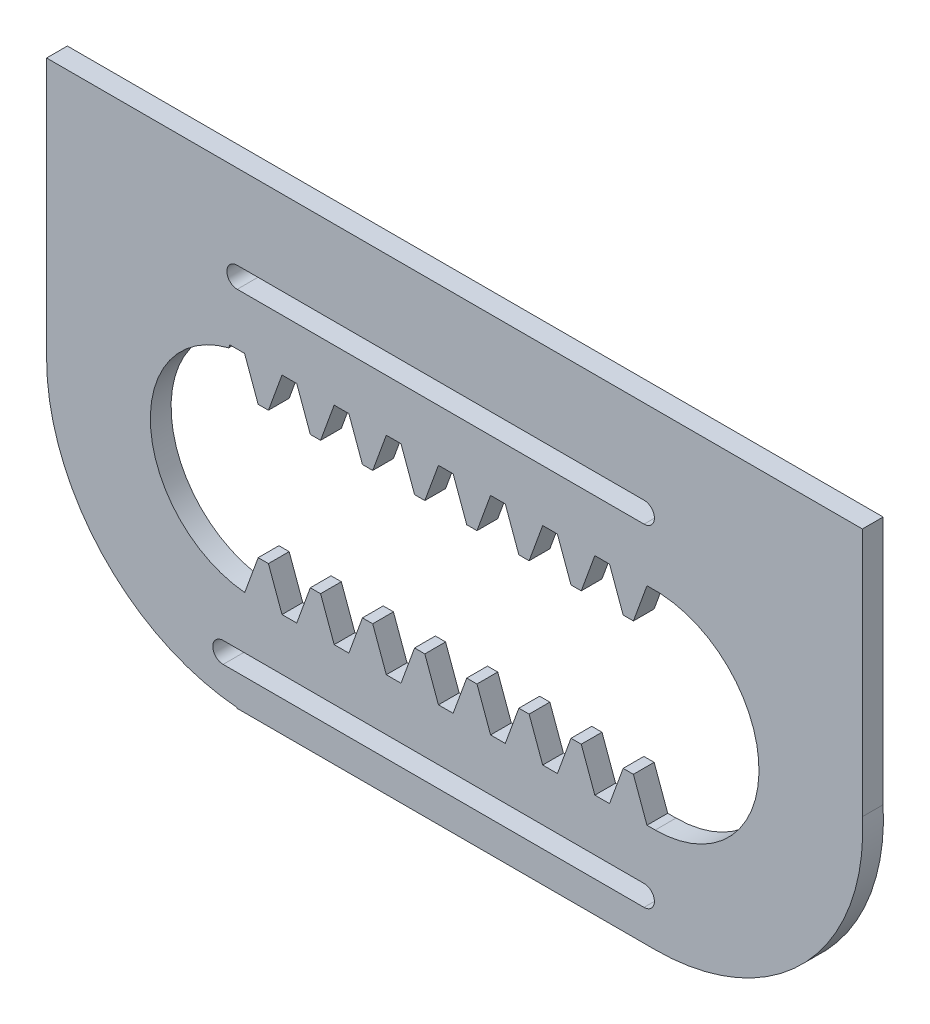
SolidWorks part; units mm, degrees
extrude "Blank" add sketch "BlankSke" against normal blind 25.4
sketch "BlankSke" plane through (0, 0, 0) normal (0, 0, 1) x (1, 0, 0)
  line L1 (0, 0) -> (127, 0)
  line L2 (0, 0) -> (0, 43.18)
  line L3 (0, 43.18) -> (127, 43.18)
  line L4 (127, 0) -> (127, 43.18)
  dimension "Length" = 127
  dimension "Blank_height" = 43.18
ref_plane "Plane1" through (0, 0, 0) normal (0, 0, 1) x (1, 0, 0)
ref_plane "Plane2" through (0, 0, 0) normal (0, 1, 0) x (1, 0, 0)
ref_plane "Plane3" through (0, 0, 0) normal (1, 0, 0) x (0, 0, -1)
other "Configuration Table"
sketch "HoldingSke" plane through (0, 0, 0) normal (0, 1, 0) x (1, 0, 0)
  line L0 (0, 0) -> (97.2876, -81.634)
  line L1 (-15, 0) -> (100, 0) construction
  line L2 (0, 0) -> (-2.1039, 2.3779)
  line L3 (0, 0) -> (-11.863, 4.5341)
  line L4 (0, 0) -> (8.5297, 1.351)
  line L5 (0, 0) -> (-23.7986, -8.8762)
  line L6 (0, 0) -> (-10.5278, -7.1032)
  line L9 (-71.009, 38.7566) -> (48.332, 82.1932)
  line L10 (-76.2, 71.12) -> (-38.1, 71.12)
  line L11 (0, 0) -> (-25.4, 0)
  line L12 (-76.2, 101.6) -> (-76.0095, 101.6)
  line L13 (24.9733, 27.94) -> (52.9518, 28.4284)
  line L14 (24.9733, 27.94) -> (24.9746, 27.94)
  line L15 (24.9733, 27.94) -> (100.4006, 29.5858)
  circle A0 centre (0, 0) radius 19.05
  circle A1 centre (0, 0) radius 19.05
  circle A2 centre (0, 0) radius 12.7
  dimension "MPH" = 38.1
  dimension "Diameter" = 38.1
  dimension "Num_teeth" = 9
  dimension "Pitch" = 127
  dimension "Show_teeth" = 400
  dimension "Thickness" = 12.7
  dimension "Ap" = 20
  dimension "Pitch_height" = 38.1
  dimension "Width" = 25.4
  dimension "Backlash" = 0.1905
  dimension "Addendum_fac" = 1
  dimension "Dedendum_fac" = 1.25
  dimension "Clearance_fac" = 0.25
  dimension "Dedendum_add" = 0.0013
  dimension "Length" = 127
sketch "TooCutSkeIll" plane through (0, 0, 0) normal (0, 0, 1) x (1, 0, 0)
  line L0 (-6.3616, 43.0463) -> (-2.5546, 32.5865)
  line L1 (-1.36, 31.75) -> (1.36, 31.75)
  line L2 (2.5546, 32.5865) -> (6.3616, 43.0463)
  line L3 (127, 43.18) -> (0, 43.18) construction
  line L4 (0, 0) -> (0, 64.897) construction
  line L5 (-13.208, 38.1) -> (12.954, 38.1) construction
  line L6 (0, 0) -> (127, 0) construction
  line L7 (4.5613, 38.1) -> (4.5613, 48.7463) construction
  line L8 (-4.5613, 38.1) -> (-4.5613, 48.7463) construction
  line L9 (6.5526, 43.18) -> (6.5526, 43.2054)
  line L10 (-6.5526, 43.18) -> (-6.5526, 43.2054)
  line L11 (-6.5526, 43.2054) -> (6.5526, 43.2054)
  arc A0 (1.36, 31.75) -> (2.5546, 32.5865) centre (1.36, 33.0213) ccw
  arc A1 (-2.5546, 32.5865) -> (-1.36, 31.75) centre (-1.36, 33.0213) ccw
  arc A2 (6.5526, 43.18) -> (6.3616, 43.0463) centre (6.5526, 42.9768) ccw
  arc A3 (-6.3616, 43.0463) -> (-6.5526, 43.18) centre (-6.5526, 42.9768) ccw
  dimension "Pitch_height" = 38.1
  dimension "Addendum_plus" = 5.1054
  dimension "Pressure_angle" = 20
  dimension "Gap_width" = 9.1226
  dimension "Dedendum" = 6.35
extrude "ToothCutIll" [suppressed] cut sketch "TooCutSkeIll" against normal through all
sketch "TooCutSkeSim" plane through (0, 0, 0) normal (0, 0, 1) x (1, 0, 0)
  line L0 (2.2501, 31.75) -> (-2.2501, 31.75)
  line L1 (6.4195, 43.2054) -> (2.2501, 31.75)
  line L2 (0, 17.4625) -> (0, 53.467) construction
  line L3 (6.4195, 43.2054) -> (-6.4195, 43.2054)
  line L6 (-6.4195, 43.2054) -> (-2.2501, 31.75)
  line L9 (-4.5613, 38.1) -> (4.5613, 38.1) construction
  line L10 (0, 0) -> (127, 0) construction
  line L11 (4.5613, 38.1) -> (4.5613, 53.467) construction
  line L12 (-4.5613, 38.1) -> (-4.5613, 53.467) construction
  dimension "Pitch_height" = 38.1
  dimension "Addendum_plus" = 5.1054
  dimension "Pressure_angle" = 20
  dimension "Gap_width" = 9.1226
  dimension "Dedendum" = 6.35
extrude "ToothCutSim" cut sketch "TooCutSkeSim" against normal through all
pattern_linear "TeethCuts" count 9 spacing 15.9593 along (1, 0, 0) of "ToothCutIll", "ToothCutSim"
sketch "Sketch3" plane through (0, 0, -25.4) normal (0, 0, -1) x (-1, 0, 0)
  line L0 (-127.9602, 63.5) -> (-5.1507, 63.5) construction
  line L1 (-127.9602, 127) -> (-5.1507, 127)
  line L2 (-127.9602, 0) -> (-5.1507, 0)
  line L3 (-61.5871, 31.75) -> (-66.0873, 31.75) construction
  line L4 (0, 0) -> (-127, 0) construction
  line L5 (-127.9602, 63.5) -> (-5.1507, 63.5) construction
  line L6 (-127.9602, 95.25) -> (-5.1507, 95.25)
  line L7 (-127.9602, 31.75) -> (-5.1507, 31.75)
  line L8 (-77.5463, 31.75) -> (-82.0466, 31.75) construction
  arc A0 (-127.9602, 127) -> (-127.9602, 0) centre (-127.9602, 63.5) ccw
  arc A1 (-5.1507, 0) -> (-5.1507, 127) centre (-5.1507, 63.5) ccw
  arc A2 (-127.9602, 95.25) -> (-127.9602, 31.75) centre (-127.9602, 63.5) ccw
  arc A3 (-5.1507, 31.75) -> (-5.1507, 95.25) centre (-5.1507, 63.5) ccw
  point P2 (-66.5555, 63.5)
  point P9 (-63.8372, 31.75)
  point P14 (-66.5555, 63.5)
  dimension "D1" = 31.75
extrude "Boss-Extrude1" add sketch "Sketch3" against normal up to surface (25.4 mm away) up to face at (63.7997, 35.0661, 0)
ref_plane "Plane4" through (0, 63.5, 0) normal (0, 1, 0) x (1, 0, 0)
mirror "Mirror1" about plane through (0, 63.5, 0) normal (0, 1, 0) of "TeethCuts", "Blank", "ToothCutSim"
sketch "Sketch4" plane through (0, 0, -25.4) normal (0, 0, -1) x (-1, 0, 0)
  line L0 (4.3146, 12.7) -> (-124.5231, 12.7) construction
  line L1 (4.3146, 9.525) -> (-124.5231, 9.525)
  line L2 (4.3146, 15.875) -> (-124.5231, 15.875)
  line L3 (0, 114.3) -> (-124.5231, 114.3) construction
  line L4 (0, 111.125) -> (-124.5231, 111.125)
  line L5 (0, 117.475) -> (-124.5231, 117.475)
  line L7 (0, 0) -> (-127.9602, 0) construction
  line L8 (0, 127) -> (-127.9602, 127) construction
  arc A0 (4.3146, 9.525) -> (4.3146, 15.875) centre (4.3146, 12.7) ccw
  arc A1 (-124.5231, 15.875) -> (-124.5231, 9.525) centre (-124.5231, 12.7) ccw
  arc A2 (0, 111.125) -> (0, 117.475) centre (0, 114.3) ccw
  arc A3 (-124.5231, 117.475) -> (-124.5231, 111.125) centre (-124.5231, 114.3) ccw
  point P2 (-60.1042, 12.7)
  point P7 (-62.2615, 114.3)
  dimension "D1" = 12.7
  dimension "D2" = 12.7
  dimension "D3" = 6.35
  dimension "D4" = 6.35
extrude "Cut-Extrude1" cut sketch "Sketch4" against normal through all
sketch "Sketch5" plane through (0, 0, 0) normal (0, 1, 0) x (1, 0, 0)
  line L0 (-58.3493, 19.05) -> (191.4602, 19.05)
  line L4 (-58.3493, 25.4) -> (-58.3493, 0) construction
  line L5 (191.4602, 0) -> (191.4602, 25.4) construction
  line L6 (0, 25.4) -> (127.9602, 25.4) construction
  line L7 (-58.3493, 19.05) -> (-58.3493, 0)
  line L8 (-58.3493, 0) -> (191.4602, 0)
  line L9 (191.4602, 0) -> (191.4602, 19.05)
  dimension "D1" = 6.35
extrude "Cut-Extrude2" cut sketch "Sketch5" along normal through all
sketch "Sketch6" plane through (0, 0, -25.4) normal (0, 0, -1) x (-1, 0, 0)
  line L0 (0, 127) -> (-127.9602, 127) construction
  line L2 (-191.3644, 117.8615) -> (-191.3644, 143.2615)
  line L3 (-191.3644, 143.2615) -> (58.3493, 143.2615)
  line L5 (-144.5313, 117.8615) -> (13.6643, 117.8615)
  line L6 (-191.3644, 117.8615) -> (-191.3644, 66.9862)
  line L7 (-191.3644, 66.9862) -> (-144.5313, 117.8615)
  line L8 (58.3493, 117.8615) -> (58.3493, 143.2615)
  line L9 (58.3493, 117.8615) -> (58.3493, 63.5)
  line L10 (58.3493, 63.5) -> (13.6643, 117.8615)
  arc A2 (-127.9602, 127) -> (-127.9602, 0) centre (-127.9602, 63.5) ccw construction
  arc A3 (0, 0.2092) -> (0, 126.7908) centre (-5.1507, 63.5) ccw construction
  point P0 (-63.9801, 127)
  dimension "D1" = 25.4
extrude "Boss-Extrude2" add sketch "Sketch6" against normal blind 6.35
equation "' \"Pitch@HoldingSke\" = 4"
equation "' \"Num_teeth@HoldingSke\" = 12"
equation "' \"Ap@HoldingSke\" =  20"
equation "' \"Ap@HoldingSke\" = 20"
equation "' \"Width@HoldingSke\" = 0.25"
equation "' \"Show_teeth@HoldingSke\" = 500"
equation "' \"Backlash@HoldingSke\" = 0.009"
equation "' \"Addendum_fac@HoldingSke\" = 1.0"
equation "' \"Dedendum_fac@HoldingSke\" = 1.25"
equation "' \"Dedendum_add@HoldingSke\" = 0.00005"
equation "' \"Clearance_fac@HoldingSke\" = 0.25"
equation "' \"Pitch_height@HoldingSke\" = 1"
equation "' \"Length@HoldingSke\" = 4.71"
equation "\"MPH@HoldingSke\" = \"Dedendum_fac@HoldingSke\" / \"Pitch@HoldingSke\" + 2 * \"Dedendum_add@HoldingSke\" + 0.002"
equation "\"MPH@HoldingSke\" = ((sgn( \"MPH@HoldingSke\" - \"Pitch_height@HoldingSke\")+1)*( \"MPH@HoldingSke\" - \"Pitch_height@HoldingSke\"))/2 + \"Pitch_height@HoldingSke\""
equation "\"Blank_height@BlankSke\" = \"Pitch_height@HoldingSke\" + \"Addendum_fac@HoldingSke\"  / \"Pitch@HoldingSke\" "
equation "\"Length@BlankSke\" =  \"Length@HoldingSke\""
equation "\"Face_width@Blank\" = \"Width@HoldingSke\""
equation "\"Pressure_angle@TooCutSkeIll\" = \"Ap@HoldingSke\""
equation "\"Addendum_plus@TooCutSkeIll\" =  \"Addendum_fac@HoldingSke\"  / \"Pitch@HoldingSke\" + 0.001"
equation "\"Dedendum@TooCutSkeIll\" = \"Dedendum_fac@HoldingSke\"  / \"Pitch@HoldingSke\""
equation "\"Pitch_height@TooCutSkeIll\" =  \"MPH@HoldingSke\""
equation "\"Gap_width@TooCutSkeIll\" = 3.14159265 / 2 / \"Pitch@HoldingSke\" + 6 * \"Backlash@HoldingSke\""
equation "\"Pressure_angle@TooCutSkeSim\" = \"Ap@HoldingSke\""
equation "\"Addendum_plus@TooCutSkeSim\" =  \"Addendum_fac@HoldingSke\"  / \"Pitch@HoldingSke\" + 0.001"
equation "\"Dedendum@TooCutSkeSim\" = \"Dedendum_fac@HoldingSke\"  / \"Pitch@HoldingSke\""
equation "\"Pitch_height@TooCutSkeSim\" =  \"MPH@HoldingSke\""
equation "\"Gap_width@TooCutSkeSim\" = 3.14159265 / 2 / \"Pitch@HoldingSke\" + 6 * \"Backlash@HoldingSke\""
equation "\"Root_fillet@TooCutSkeIll\" = \"Clearance_fac@HoldingSke\" / \"Pitch@HoldingSke\" + \"Dedendum_add@HoldingSke\""
equation "\"Break_rad@TooCutSkeIll\" = 0.02 / \"Pitch@HoldingSke\" * 2"
equation "\"Linear_pitch@TeethCuts\" = 3.14159265 / \"Pitch@HoldingSke\""
equation "\"Num_teeth@HoldingSke\" = int( ( \"Length@HoldingSke\" + 0 ) / (3.14159265 / \"Pitch@HoldingSke\")) + 0.9999  + 1"
equation " \"Num_teeth@TeethCuts\" = int( \"Show_teeth@HoldingSke\" ) + 1"
equation " \"Num_teeth@TeethCuts\" = ((sgn( \"Num_teeth@TeethCuts\" - \"Num_teeth@HoldingSke\" )-1)*( \"Num_teeth@TeethCuts\" - \"Num_teeth@HoldingSke\" ))/-2+ \"Num_teeth@HoldingSke\""
equation " \"Num_teeth@TeethCuts\" = ((sgn( \"Num_teeth@TeethCuts\" - 2.0)+1)*( \"Num_teeth@TeethCuts\" - 2.0))/2 +2.0"
